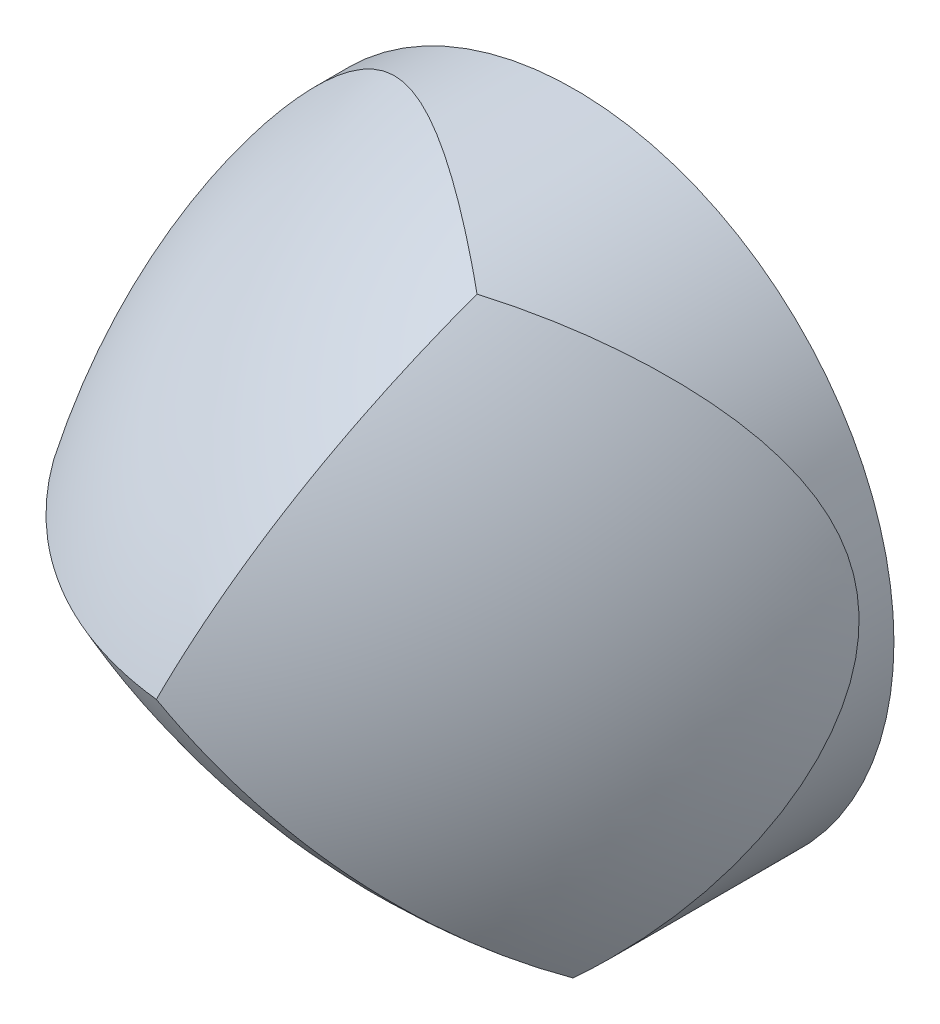
SolidWorks part; units mm, degrees
ref_plane "Front Plane" through (0, 0, 0) normal (0, 0, 1) x (1, 0, 0)
ref_plane "Top Plane" through (0, 0, 0) normal (0, 1, 0) x (1, 0, 0)
ref_plane "Right Plane" through (0, 0, 0) normal (1, 0, 0) x (0, 0, -1)
sketch "Sketch1" plane through (0, 0, 0) normal (0, 0, 1) x (1, 0, 0)
  circle A2 centre (0, 0) radius 152.4
extrude "Boss-Extrude1" add sketch "Sketch1" along normal blind 300
sketch "Sketch2" plane through (0, 0, -90.9) normal (0.766, 0.6428, 0) x (-0.6428, 0.766, 0)
  line L1 (-147.5708, -21.8) -> (-141.1044, -21.8) construction
  line L2 (-144.3376, -21.8) -> (-144.3376, 16.4) construction
  line L3 (-144.3376, -293.6) -> (-144.3376, -593.6)
  line L4 (-144.3376, 326.4) -> (-144.3376, 626.4)
  arc A0 (-144.3376, -293.6) -> (-144.3376, 326.4) centre (-144.3376, 16.4) ccw
  arc A1 (-144.3376, -593.6) -> (-144.3376, 626.4) centre (-144.3376, 16.4) ccw
  circle A2 centre (-144.3376, 16.4) radius 610 construction
  circle A3 centre (-144.3376, 16.4) radius 310 construction
  dimension "D1" = 620
  dimension "D3" = 300
revolve "Cut-Revolve1" cut sketch "Sketch2" angle 360 about L2
pattern_circular "CirPattern1" count 3 every 120 about axis through (0, 0, 0) along (0, 0, 1) of "Cut-Revolve1"
